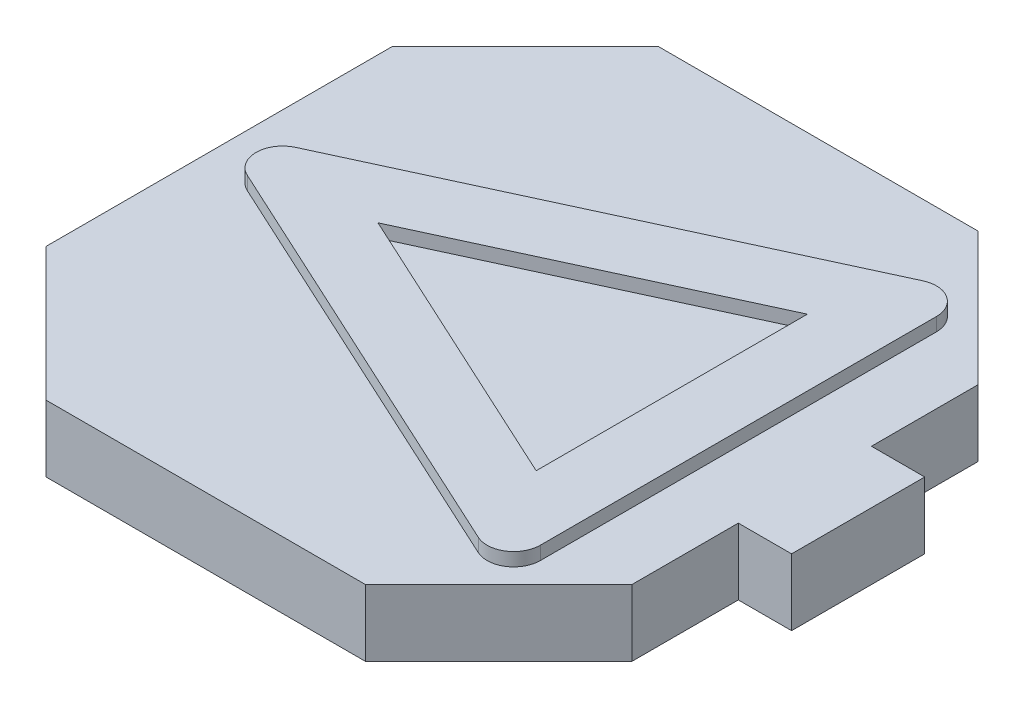
SolidWorks part; units mm, degrees
ref_plane "Plan de face" through (0, 0, 0) normal (0, 0, 1) x (1, 0, 0)
ref_plane "Plan de dessus" through (0, 0, 0) normal (0, 1, 0) x (1, 0, 0)
ref_plane "Plan de droite" through (0, 0, 0) normal (1, 0, 0) x (0, 0, -1)
sketch "Esquisse1" plane through (0, 0, 0) normal (0, 1, 0) x (1, 0, 0)
  line L0 (22, 13) -> (12.003, 23)
  line L1 (22, 13) -> (22, 5)
  line L2 (-22, -13) -> (-22, 13)
  line L3 (22, 5) -> (26, 5)
  line L4 (22, -5) -> (22, -13)
  line L5 (-22, -13) -> (22, 13) construction
  line L6 (-22, 13) -> (22, -13) construction
  line L7 (12.003, 23) -> (-12.003, 23)
  line L8 (-12.003, 23) -> (-22, 13)
  line L9 (-22, -13) -> (-12.003, -23)
  line L10 (-12.003, -23) -> (12.003, -23)
  line L11 (12.003, -23) -> (22, -13)
  line L12 (0, 23) -> (0, 0) construction
  line L13 (0, 0) -> (0, -23) construction
  line L14 (22, -5) -> (26, -5)
  line L15 (26, 5) -> (26, -5)
  point P1 (0, 0)
  dimension "D1" = 26
  dimension "D2" = 44
  dimension "D3" = 23
  dimension "D4" = 23
  dimension "D5" = 14.14
  dimension "D6" = 14.14
  dimension "D7" = 14.14
  dimension "D8" = 14.14
  dimension "D9" = 8
  dimension "D10" = 8
  dimension "D11" = 4
extrude "Boss.-Extru.1" add sketch "Esquisse1" along normal blind 5
sketch "Esquisse2" plane through (0, 5, 0) normal (0, 1, 0) x (1, 0, 0)
  line L0 (17.0015, -18) -> (17.0015, 18)
  line L1 (12.003, -23) -> (22, -13) construction
  line L2 (22, 13) -> (12.003, 23) construction
  line L3 (17.0015, 18) -> (-22, 0)
  line L4 (-22, 13) -> (-22, -13) construction
  line L5 (-22, 0) -> (17.0015, -18)
  line L6 (-10.0681, 0) -> (12.0015, -10.1856)
  line L7 (12.0015, -10.1856) -> (12.0015, 10.1856)
  line L8 (12.0015, 10.1856) -> (-10.0681, 0)
  dimension "D1" = 5
  dimension "D2" = 5
  dimension "D3" = 5
extrude "Boss.-Extru.2" add sketch "Esquisse2" along normal blind 1
sketch "Esquisse3" plane through (0, 0, 0) normal (0, -1, 0) x (1, 0, 0)
  line L0 (-12.003, 23) -> (12.003, 23) construction
  line L1 (-16, 17) -> (-10.8, 17)
  line L2 (-16, 17) -> (-16, 11.8)
  line L3 (-16, 11.8) -> (-10.8, 11.8)
  line L4 (-10.8, 17) -> (-10.8, 11.8)
  line L5 (-16, 17) -> (-10.8, 11.8) construction
  line L6 (-16, 11.8) -> (-10.8, 17) construction
  line L8 (-22, -13) -> (-22, 13) construction
  line L9 (12.003, -23) -> (-12.003, -23) construction
  line L10 (-16, -17) -> (-10.8, -17)
  line L11 (-16, -17) -> (-16, -11.8)
  line L12 (-16, -11.8) -> (-10.8, -11.8)
  line L13 (-10.8, -17) -> (-10.8, -11.8)
  line L14 (-16, -17) -> (-10.8, -11.8) construction
  line L15 (-16, -11.8) -> (-10.8, -17) construction
  line L16 (10.8, -11.8) -> (16, -11.8)
  line L17 (10.8, -11.8) -> (10.8, -17)
  line L18 (10.8, -17) -> (16, -17)
  line L19 (16, -11.8) -> (16, -17)
  line L20 (10.8, -11.8) -> (16, -17) construction
  line L21 (10.8, -17) -> (16, -11.8) construction
  line L22 (10.8, 11.8) -> (16, 11.8)
  line L23 (10.8, 11.8) -> (10.8, 17)
  line L24 (10.8, 17) -> (16, 17)
  line L25 (16, 11.8) -> (16, 17)
  line L26 (10.8, 11.8) -> (16, 17) construction
  line L27 (10.8, 17) -> (16, 11.8) construction
  line L28 (22, -5) -> (22, -13) construction
  line L29 (22, 13) -> (22, 5) construction
  line L31 (-2.5, -2.5) -> (2.5, -2.5)
  line L32 (-2.5, -2.5) -> (-2.5, 2.5)
  line L33 (-2.5, 2.5) -> (2.5, 2.5)
  line L34 (2.5, -2.5) -> (2.5, 2.5)
  line L35 (-2.5, -2.5) -> (2.5, 2.5) construction
  line L36 (-2.5, 2.5) -> (2.5, -2.5) construction
  point P0 (-13.4, 14.4)
  point P9 (-13.4, -14.4)
  point P14 (13.4, -14.4)
  point P19 (13.4, 14.4)
  point P30 (0, 0)
  dimension "D1" = 5.2
  dimension "D2" = 5.2
  dimension "D3" = 6
  dimension "D4" = 6
  dimension "D5" = 5.2
  dimension "D6" = 5.2
  dimension "D7" = 5.2
  dimension "D8" = 5.2
  dimension "D9" = 5.2
  dimension "D10" = 5.2
  dimension "D11" = 6
  dimension "D12" = 6
  dimension "D13" = 6
  dimension "D14" = 6
  dimension "D15" = 6
  dimension "D16" = 6
  dimension "D17" = 5
  dimension "D18" = 5
  dimension "D19" = 20.5
  dimension "D20" = 20.5
  dimension "D21" = 19.5
  dimension "D22" = 19.5
extrude "Enlèv. mat.-Extru.1" cut sketch "Esquisse3" against normal blind 4.8
fillet "Congé4" radius 2 3 edges at (-22, 5.5, 0) (17.0015, 5.5, -18) (17.0015, 5.5, 18)
